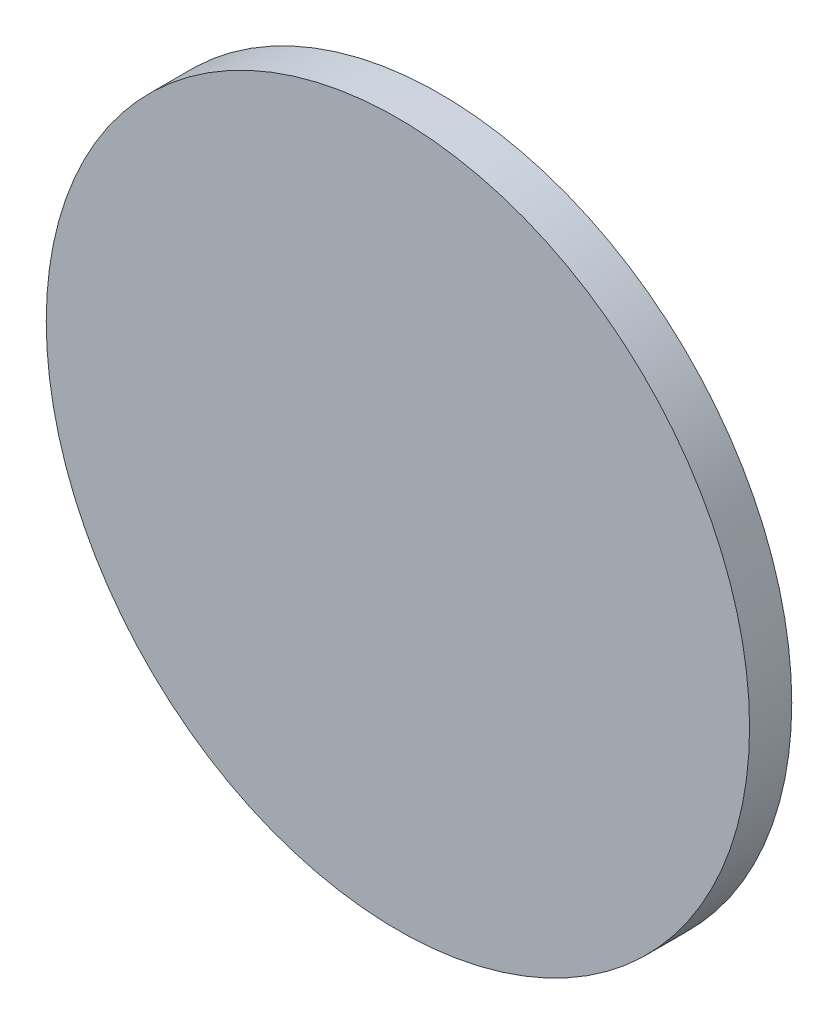
SolidWorks part; units mm, degrees
ref_plane "前视基准面" through (0, 0, 0) normal (0, 0, 1) x (1, 0, 0)
ref_plane "上视基准面" through (0, 0, 0) normal (0, 1, 0) x (1, 0, 0)
ref_plane "右视基准面" through (0, 0, 0) normal (1, 0, 0) x (0, 0, -1)
sketch "草图1" plane through (0, 0, 0) normal (0, 0, 1) x (1, 0, 0)
  circle A0 centre (0, 0) radius 25
  dimension "D1" = 50
extrude "凸台-拉伸1" add sketch "草图1" along normal blind 3 contours A0
